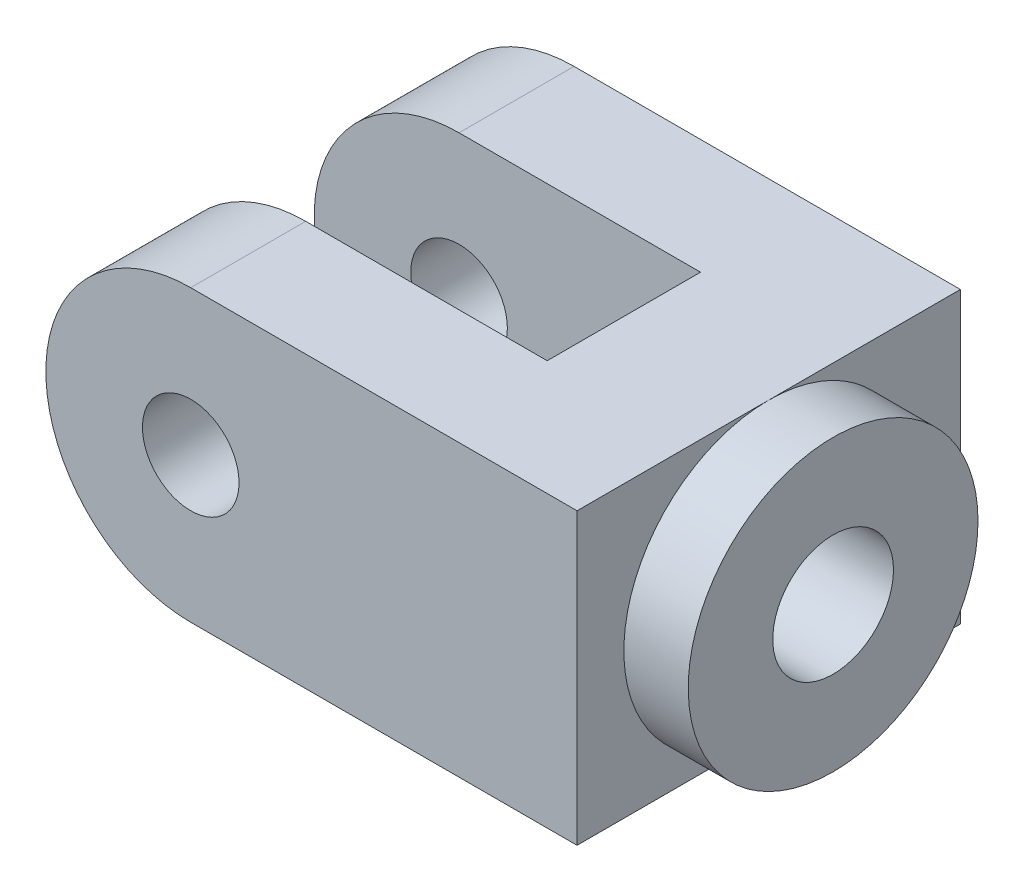
SolidWorks part; units mm, degrees
ref_plane "Front Plane" through (0, 0, 0) normal (0, 0, 1) x (1, 0, 0)
ref_plane "Top Plane" through (0, 0, 0) normal (0, 1, 0) x (1, 0, 0)
ref_plane "Right Plane" through (0, 0, 0) normal (1, 0, 0) x (0, 0, -1)
sketch "Sketch1" plane through (0, 0, 0) normal (0, 0, 1) x (1, 0, 0)
  line L1 (-66, -36) -> (66, -36)
  line L2 (-66, -36) -> (-66, 36)
  line L3 (-66, 36) -> (66, 36)
  line L4 (66, -36) -> (66, 36)
  line L5 (-66, -36) -> (66, 36) construction
  line L6 (-66, 36) -> (66, -36) construction
  point P0 (0, 0)
  dimension "D1" = 132
  dimension "D2" = 72
extrude "Boss-Extrude1" add sketch "Sketch1" along normal mid plane 95.25
sketch "Sketch2" plane through (0, 0, 47.625) normal (0, 0, 1) x (1, 0, 0)
  line L0 (66, 36) -> (-66, 36) construction
  line L1 (-66, -36) -> (66, -36) construction
  line L2 (-66, 36) -> (-66, -36) construction
  arc A0 (-30, 36) -> (-30, -36) centre (-30, 0) ccw
  dimension "D1" = 36
extrude "Cut-Extrude1" cut sketch "Sketch2" against normal through all and the other way through all flip side to cut
sketch "Sketch3" plane through (0, 36, 0) normal (0, 1, 0) x (1, 0, 0)
  line L0 (-66, 47.625) -> (-66, -47.625) construction
  line L1 (30, 19.05) -> (-66, 19.05)
  line L2 (30, 19.05) -> (30, -19.05)
  line L3 (30, -19.05) -> (-66, -19.05)
  line L4 (-66, 19.05) -> (-66, -19.05)
  line L5 (-66, -47.625) -> (-30, -47.625) construction
  line L6 (-30, -47.625) -> (-30, 47.625) construction
  dimension "D1" = 38.1
  dimension "D2" = 28.575
  dimension "D3" = 60
extrude "Cut-Extrude2" cut sketch "Sketch3" against normal through all
sketch "Sketch4" plane through (66, 0, 0) normal (1, 0, 0) x (0, 0, -1)
  circle A0 centre (0, 0) radius 15
  dimension "D1" = 30
extrude "Cut-Extrude3" cut sketch "Sketch4" against normal through all
sketch "Sketch5" plane through (66, 0, 0) normal (1, 0, 0) x (0, 0, -1)
  circle A0 centre (0, 0) radius 36
  circle A1 centre (0, 0) radius 15 construction
  circle A2 centre (0, 0) radius 15
  dimension "D1" = 72
extrude "Boss-Extrude2" add sketch "Sketch5" along normal blind 16
sketch "Sketch6" plane through (0, 0, 47.625) normal (0, 0, 1) x (1, 0, 0)
  circle A0 centre (-30, 0) radius 12
  arc A1 (-30, 36) -> (-30, -36) centre (-30, 0) ccw construction
  dimension "D1" = 24
extrude "Cut-Extrude4" cut sketch "Sketch6" against normal through all
